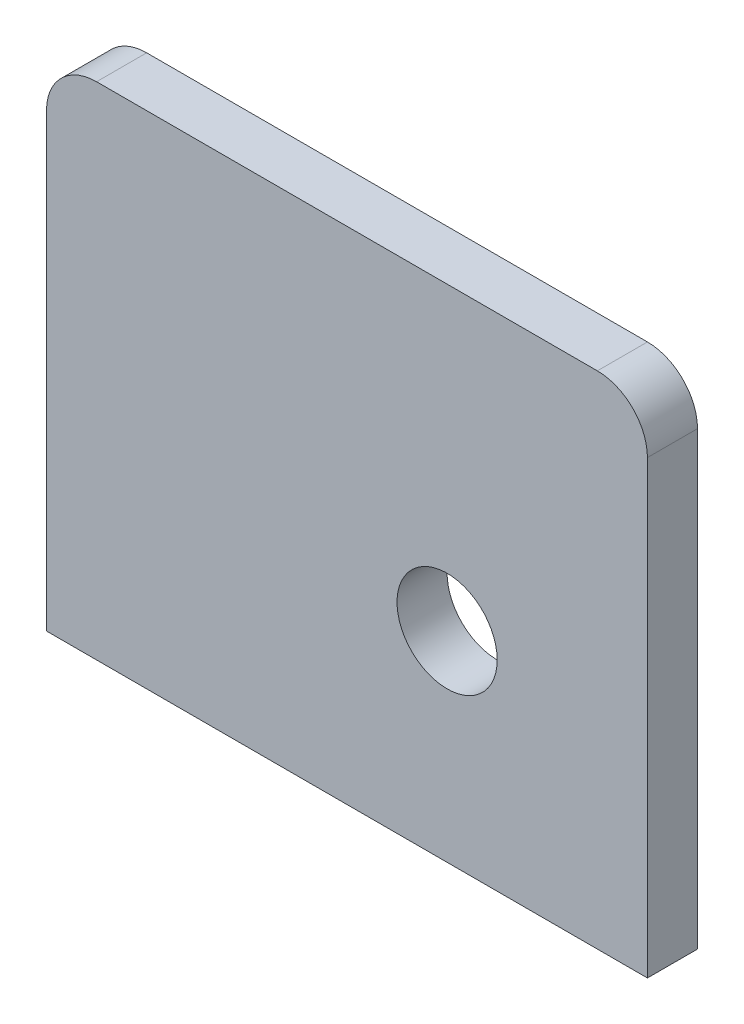
SolidWorks part; units mm, degrees
ref_plane "Front Plane" through (0, 0, 0) normal (0, 0, 1) x (1, 0, 0)
ref_plane "Top Plane" through (0, 0, 0) normal (0, 1, 0) x (1, 0, 0)
ref_plane "Right Plane" through (0, 0, 0) normal (1, 0, 0) x (0, 0, -1)
sketch "Sketch1" plane through (0, 0, 0) normal (0, 0, 1) x (1, 0, 0)
  line L0 (0, 0) -> (76.2, 0)
  line L1 (0, 0) -> (0, 63.5)
  line L2 (0, 63.5) -> (76.2, 63.5)
  line L3 (76.2, 63.5) -> (76.2, 0)
extrude "Boss-Extrude1" add sketch "Sketch1" along normal blind 6.35
sketch "Sketch2" plane through (0, 0, 6.35) normal (0, 0, 1) x (1, 0, 0)
  circle A0 centre (50.8, 25.4) radius 6.35
  point P0 (50.8, 25.4)
fillet "Fillet1" radius 6.35 1 edges at (0, 63.5, 3.175)
fillet "Fillet2" radius 6.35 1 edges at (76.2, 63.5, 3.175)
extrude "Cut-Extrude1" cut sketch "Sketch2" against normal through all contours A0
